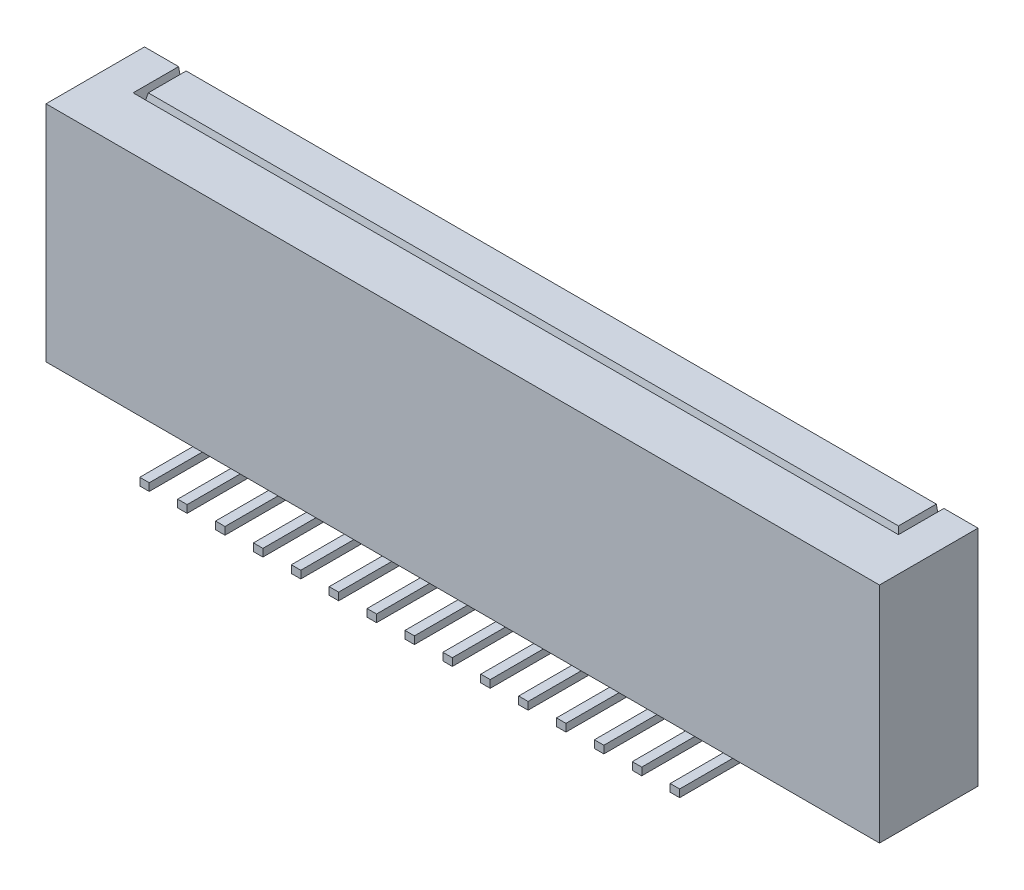
SolidWorks part; units mm, degrees
ref_plane "Plano frontal" through (0, 0, 0) normal (0, 0, 1) x (1, 0, 0)
ref_plane "Plano superior" through (0, 0, 0) normal (0, 1, 0) x (1, 0, 0)
ref_plane "Plano direito" through (0, 0, 0) normal (1, 0, 0) x (0, 0, -1)
sketch "Esboço1" plane through (0, 0, 0) normal (0, 0, 1) x (1, 0, 0)
  line L1 (-22, -2.974) -> (0, -2.974)
  line L2 (-22, -2.974) -> (-22, -8.874)
  line L3 (-22, -8.874) -> (0, -8.874)
  line L4 (0, -2.974) -> (0, -8.874)
  dimension "D1" = 22
  dimension "D2" = 5.9
extrude "Ressalto-extrusão1" add sketch "Esboço1" along normal blind 2.6 separate body
sketch "Esboço2" plane through (0, -2.974, 0) normal (0, 1, 0) x (1, 0, 0)
  line L1 (-21, -1.1) -> (-1, -1.1) construction
  line L2 (-21, -1.1) -> (-21, 0) construction
  line L3 (-21.1, -1.2) -> (-21.1, 0)
  line L4 (-1, -1.1) -> (-1, 0) construction
  line L5 (-22, -2.6) -> (-22, 0) construction
  line L6 (-21.1, -1.2) -> (-0.9, -1.2)
  line L7 (-0.9, -1.2) -> (-0.9, 0)
  line L8 (-20.9, -1) -> (-20.9, 0)
  line L9 (-20.9, -1) -> (-1.1, -1)
  line L10 (-1.1, -1) -> (-1.1, 0)
  arc A0 (-21.1, 0) -> (-20.9, 0) centre (-21, 0) cw
  arc A1 (-0.9, 0) -> (-1.1, 0) centre (-1, 0) ccw
  dimension "D1" = 20
  dimension "D2" = 1.1
  dimension "D3" = 1
  dimension "D4" = 0.1
  dimension "D5" = 0.1
extrude "Corte-extrusão1" cut sketch "Esboço2" against normal blind 1 draft 12
sketch "Esboço3" plane through (0, -8.874, 0) normal (0, -1, 0) x (1, 0, 0)
  line L0 (-22, 2.6) -> (0, 2.6) construction
  line L1 (-18.125, 2) -> (-17.875, 2)
  line L2 (-18.125, 2) -> (-18.125, 4)
  line L3 (-18.125, 4) -> (-17.875, 4)
  line L4 (-17.875, 2) -> (-17.875, 4)
  line L5 (-22, 2.6) -> (-22, 0) construction
  dimension "D1" = 0.25
  dimension "D2" = 1.4
  dimension "D3" = 2
  dimension "D4" = 3.875
extrude "Ressalto-extrusão2" add sketch "Esboço3" along normal blind 0.2
pattern_linear "Padrão linear1" count 15 spacing 1 along (1, 0, 0) of "Ressalto-extrusão2"
ref_plane "Plano1" through (0, 0, 1.3) normal (0, 0, -1) x (-1, 0, 0)
mirror "Espelhar1" about plane through (0, 0, 1.3) normal (0, 0, -1) of "Padrão linear1", "Ressalto-extrusão2"
